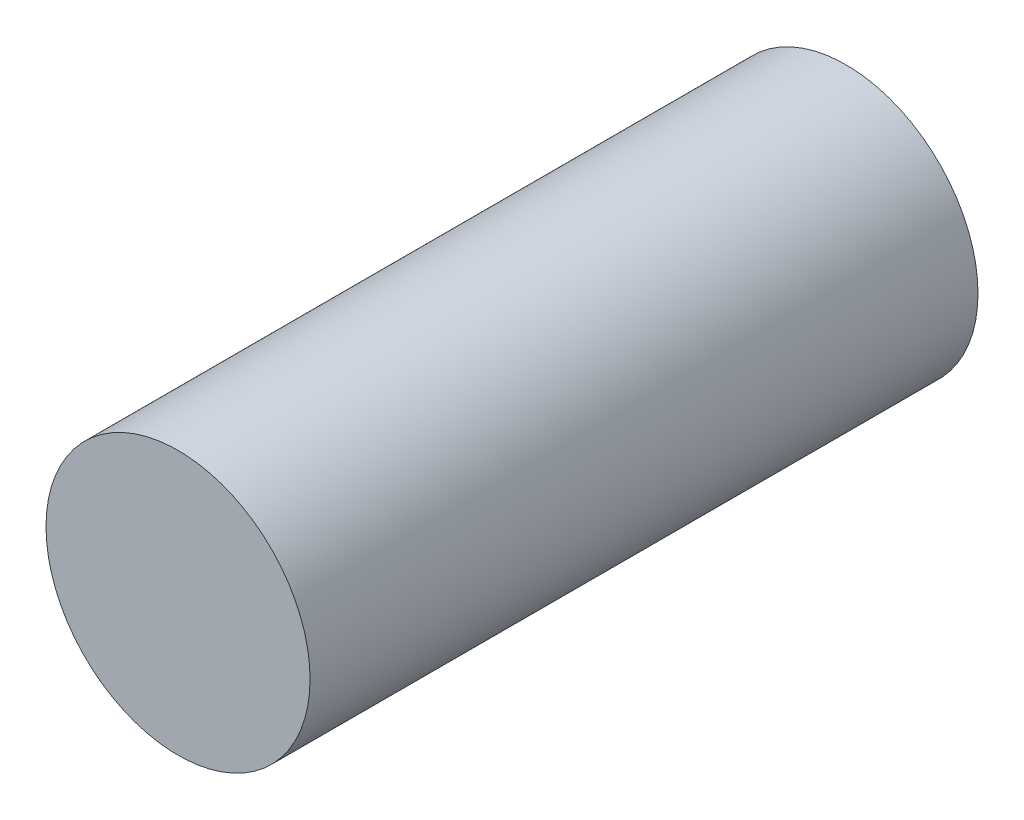
SolidWorks part; units mm, degrees
ref_plane "Plan de face" through (0, 0, 0) normal (0, 0, 1) x (1, 0, 0)
ref_plane "Plan de dessus" through (0, 0, 0) normal (0, 1, 0) x (1, 0, 0)
ref_plane "Plan de droite" through (0, 0, 0) normal (1, 0, 0) x (0, 0, -1)
sketch "Main-Sketch" plane through (0, 0, 0) normal (0, 0, 1) x (1, 0, 0)
  circle A0 centre (0, 0) radius 8.5
  point P2 (0, 0)
  dimension "D1" = 17
extrude "Main-Extrusion" add sketch "Main-Sketch" along normal blind 43
